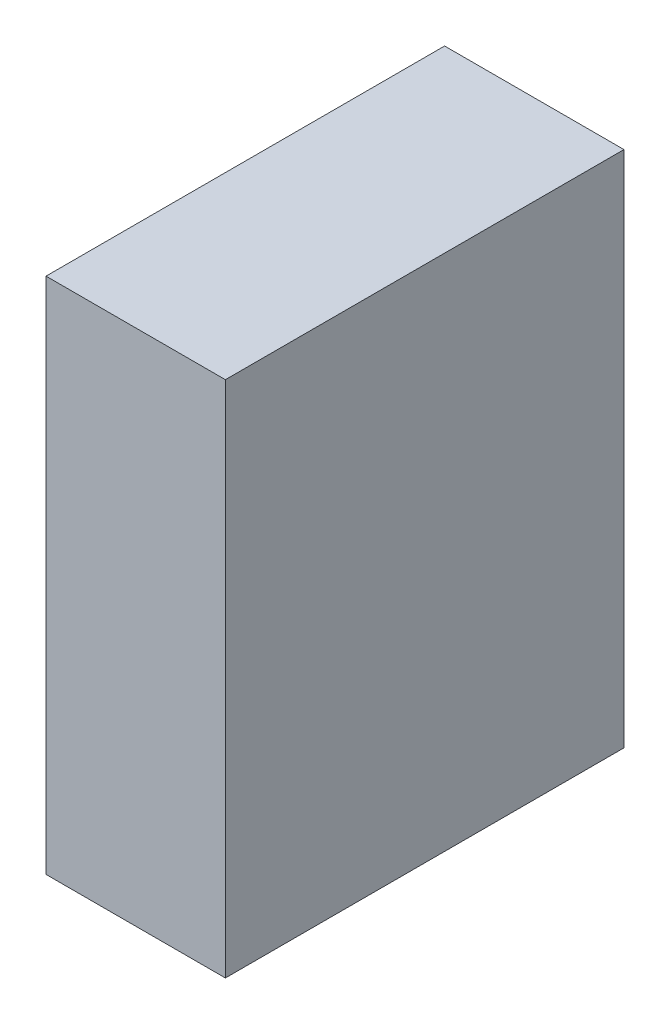
SolidWorks part; units mm, degrees
material "Custom Plastic (3)"
ref_plane "Front Plane" through (0, 0, 0) normal (0, 0, 1) x (1, 0, 0)
ref_plane "Top Plane" through (0, 0, 0) normal (0, 1, 0) x (1, 0, 0)
ref_plane "Right Plane" through (0, 0, 0) normal (1, 0, 0) x (0, 0, -1)
sketch "Motor Cross Section" plane through (0, 0, 0) normal (1, 0, 0) x (0, 0, -1)
  line L1 (-127, -165.1) -> (127, -165.1)
  line L2 (-127, -165.1) -> (-127, 165.1)
  line L3 (-127, 165.1) -> (127, 165.1)
  line L4 (127, -165.1) -> (127, 165.1)
  line L5 (-127, -165.1) -> (127, 165.1) construction
  line L6 (-127, 165.1) -> (127, -165.1) construction
  point P0 (0, 0)
  dimension "D1" = 254
  dimension "D2" = 330.2
extrude "Motor" add sketch "Motor Cross Section" along normal mid plane 114.3
